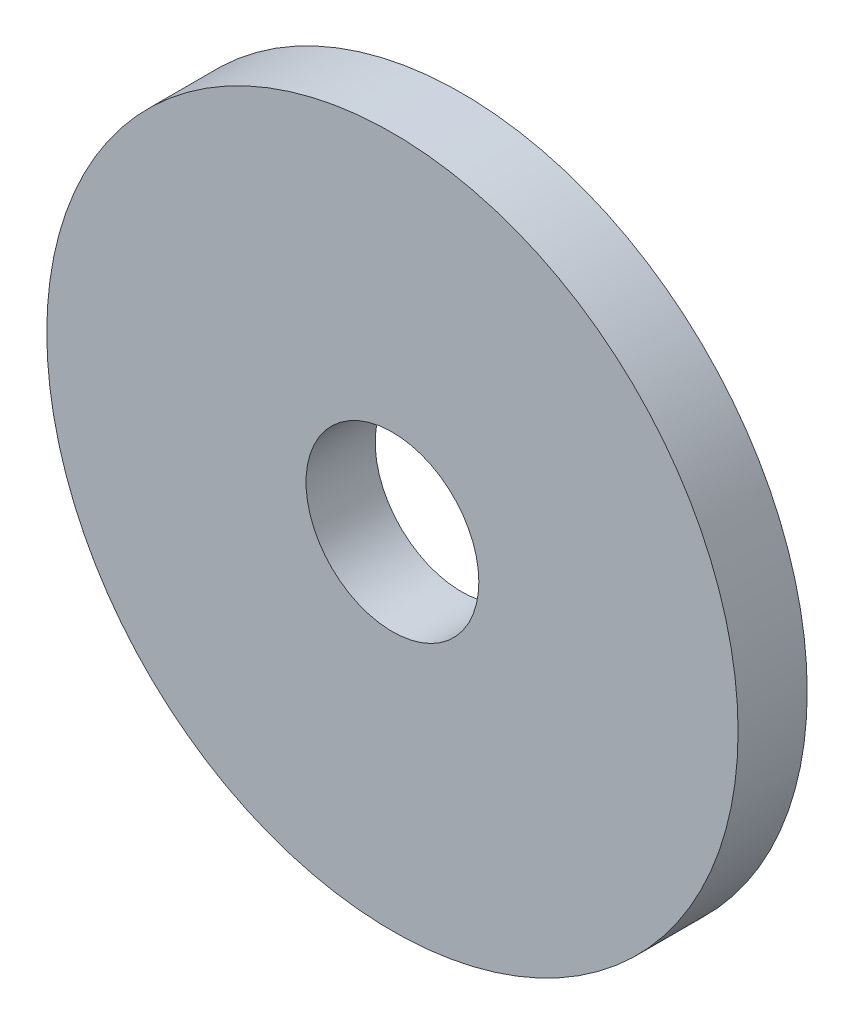
SolidWorks part; units mm, degrees
ref_plane "Front Plane" through (0, 0, 0) normal (0, 0, 1) x (1, 0, 0)
ref_plane "Top Plane" through (0, 0, 0) normal (0, 1, 0) x (1, 0, 0)
ref_plane "Right Plane" through (0, 0, 0) normal (1, 0, 0) x (0, 0, -1)
sketch "Sketch1" plane through (0, 0, 0) normal (0, 0, 1) x (1, 0, 0)
  circle A0 centre (0, 0) radius 20
extrude "Boss-Extrude1" add sketch "Sketch1" along normal blind 4
sketch "Sketch2" plane through (0, 0, 4) normal (0, 0, 1) x (1, 0, 0)
  circle A0 centre (0, 0) radius 5
extrude "Cut-Extrude1" cut sketch "Sketch2" against normal blind 4
